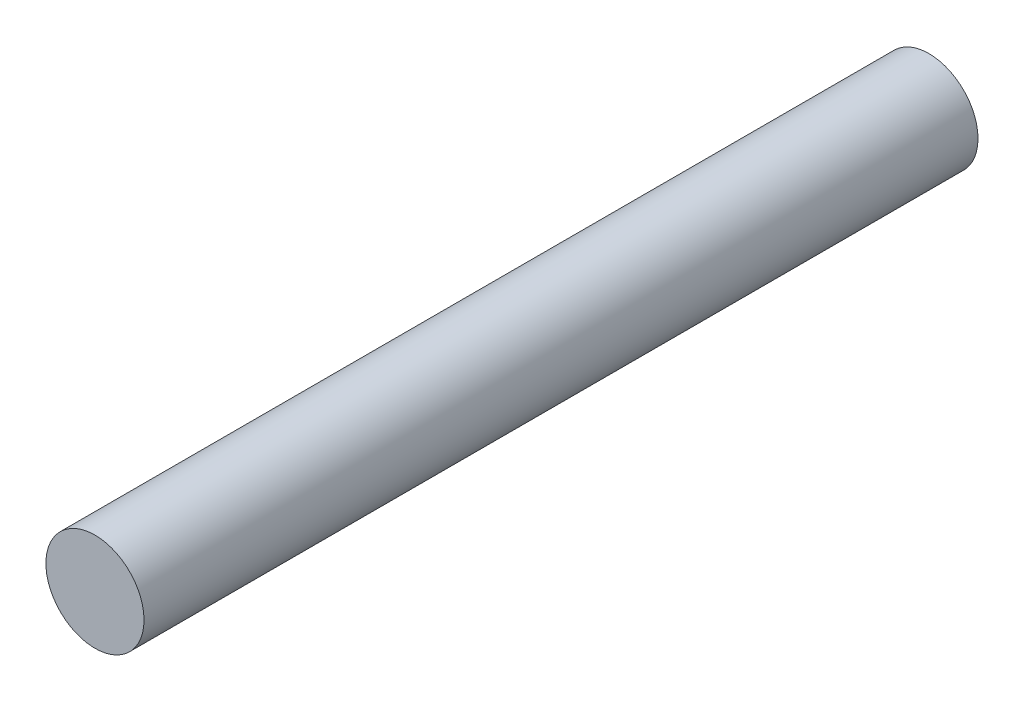
SolidWorks part; units mm, degrees
material "1.5714 (16NiCr4)"
ref_plane "Plan de face" through (0, 0, 0) normal (0, 0, 1) x (1, 0, 0)
ref_plane "Plan de dessus" through (0, 0, 0) normal (0, 1, 0) x (1, 0, 0)
ref_plane "Plan de droite" through (0, 0, 0) normal (1, 0, 0) x (0, 0, -1)
sketch "Esquisse1" plane through (0, 0, 0) normal (0, 0, 1) x (1, 0, 0)
  circle A0 centre (0, 0) radius 5
  dimension "D1" = 10
extrude "Boss.-Extru.1" add sketch "Esquisse1" along normal blind 85
